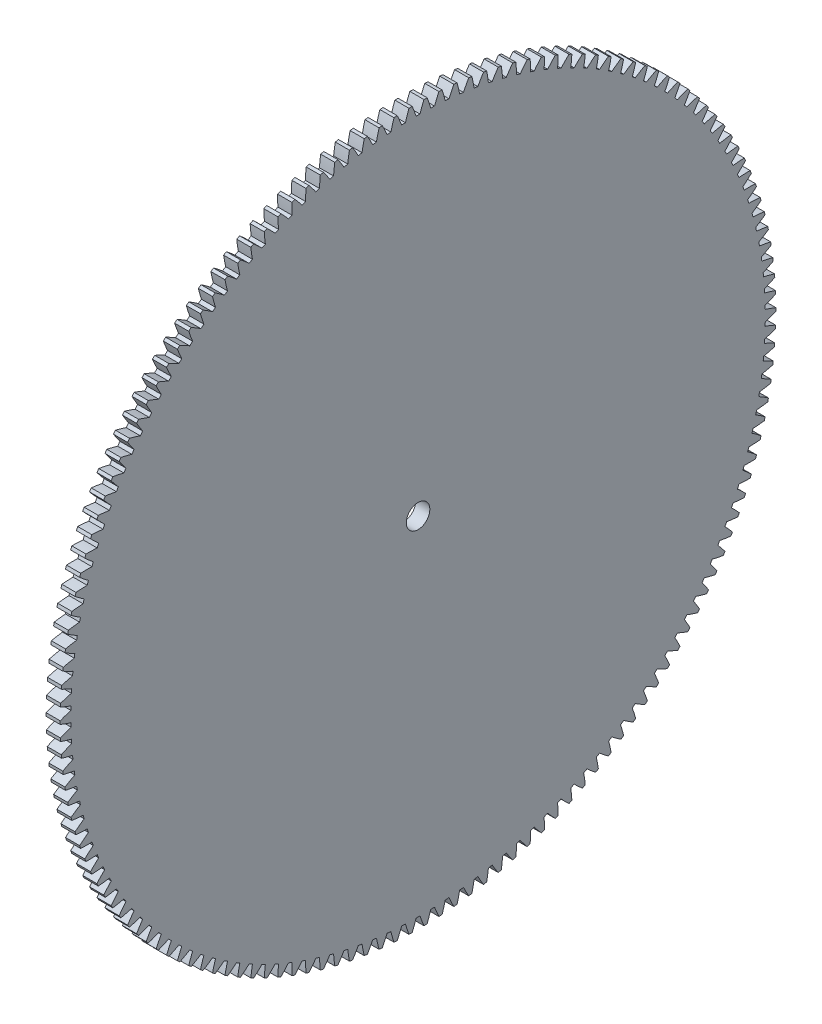
SolidWorks part; units mm, degrees
ref_plane "Plane1" through (0, 0, 0) normal (0, 0, 1) x (1, 0, 0)
ref_plane "Plane2" through (0, 0, 0) normal (0, 1, 0) x (1, 0, 0)
ref_plane "Plane3" through (0, 0, 0) normal (1, 0, 0) x (0, 0, -1)
sketch "HoldingSke" plane through (0, 0, 0) normal (0, 1, 0) x (1, 0, 0)
  line L0 (0, 0) -> (-0.866, -0.5)
  line L1 (-15, 0) -> (100, 0) construction
  line L2 (0, 0) -> (-2.1039, 2.3779)
  line L3 (0, 0) -> (-11.863, 4.5341)
  line L4 (0, 0) -> (-7.479, 4.318)
  line L5 (0, 0) -> (-46.8476, -17.4728)
  line L6 (0, 0) -> (-2.4869, -1.6779)
  line L7 (-2.1039, 2.3779) -> (8.6586, 51.2059)
  line L8 (-76.2, 54.61) -> (-75.3, 54.61)
  line L9 (-71.009, 38.7566) -> (-53.1078, 45.2721)
  line L10 (-76.2, 71.12) -> (104.1128, 71.12)
  line L11 (0, 0) -> (-3, 0)
  line L12 (-76.2, 101.6) -> (-76.162, 101.6)
  line L13 (24.9733, 27.94) -> (52.9518, 28.4284)
  line L14 (24.9733, 27.94) -> (24.9743, 27.94)
  line L15 (24.9733, 27.94) -> (100.4006, 29.5858)
  line L16 (-63.627, -1) -> (-12.827, -1)
  circle A0 centre (0, 0) radius 2.5
  circle A1 centre (0, 0) radius 37.5
  circle A2 centre (0, 0) radius 37.5
  circle A3 centre (0, 0) radius 2.5
  dimension "MHD" = 75
  dimension "Hub_dia" = 75
  dimension "Bore" = 5
  dimension "MBD" = 5
  dimension "Num_teeth" = 150
  dimension "Pitch_radius" = 180.3128
  dimension "Pitch" = 1
  dimension "Width" = 3
  dimension "Overall_len" = 50
  dimension "Show_teeth" = 150
  dimension "Thickness" = 3
  dimension "OAL" = 50.0001
  dimension "T_dim" = 0.9
  dimension "Ap" = 20
  dimension "H" = 19.05
  dimension "Backlash" = 0.038
  dimension "Addendum_fac" = 1
  dimension "Dedendum_fac" = 1.25
  dimension "Clearance_fac" = 0.25
  dimension "Dedendum_add" = 0.001
  dimension "Module" = 1
sketch "BasProSke" plane through (0, 0, 0) normal (0, 1, 0) x (1, 0, 0)
  line L0 (-10, 0) -> (60, 0) construction
  line L1 (0, 0) -> (0, 76)
  line L2 (0, 0) -> (3, 0)
  line L3 (3, 0) -> (3, 76)
  line L4 (3, 76) -> (0, 76)
  dimension "Diameter" = 152
  dimension "Thickness" = 3
revolve "Base-Revolve" add sketch "BasProSke" angle 360 about L0
sketch "TooCutSke" plane through (0, 0, 0) normal (1, 0, 0) x (0, 0, -1)
  line L1 (0, 0) -> (0, 107) construction
  line L2 (0, 0) -> (-0.8519, 74.9952) construction
  line L3 (0, 0) -> (-3.1412, 149.9602) construction
  line L4 (-0.8519, 74.9952) -> (-1.5706, 74.9801) construction
  arc A0 (0.4067, 73.7479) -> (-0.4067, 73.7479) centre (0, 0) ccw
  arc A1 (1.263, 76.0149) -> (-1.263, 76.0149) centre (0, 0) ccw
  circle A2 centre (0, 0) radius 75 construction
  circle A3 centre (0, 0) radius 70.4769 construction
  arc A4 (-0.4067, 73.7479) -> (-1.263, 76.0149) centre (-28.8767, 64.2895) ccw
  arc A5 (1.263, 76.0149) -> (0.4067, 73.7479) centre (28.8767, 64.2895) ccw
  dimension "Root_dia" = 147.498
  dimension "Overcut_dia" = 152.0508
  dimension "Pitch_dia" = 150
  dimension "Base_dia" = 140.9539
  dimension "Flank_rad" = 30
  dimension "Half_ang" = 1.2
  dimension "Half_CT" = 0.7189
extrude "ToothCut" cut sketch "TooCutSke" along normal through all
fillet "Breaks" [suppressed] radius 0.02
fillet "RootFillets" [suppressed] radius 0.251
pattern_circular "TeethCuts" count 150 every 2.4 about axis through (-10, 0, 0) along (1, 0, 0) of "ToothCut", "RootFillets", "Breaks"
sketch "HubNeaOneSke" plane through (0, 0, 0) normal (-1, 0, 0) x (0, 0, 1)
  circle A0 centre (0, 0) radius 37.5
  dimension "Diameter" = 75
extrude "HubNearOne" [suppressed] add sketch "HubNeaOneSke" along normal blind 47.0001
sketch "HubNeaBotSke" plane through (0, 0, 0) normal (-1, 0, 0) x (0, 0, 1)
  circle A0 centre (0, 0) radius 37.5
  dimension "Diameter" = 75
extrude "HubNearBoth" [suppressed] add sketch "HubNeaBotSke" along normal blind 23.5
ref_plane "FarPln" through (3, 0, 0) normal (1, 0, 0) x (0, 0, -1)
sketch "HubFarSke" plane through (3, 0, 0) normal (1, 0, 0) x (0, 0, -1)
  circle A0 centre (0, 0) radius 37.5
  dimension "Diameter" = 75
extrude "HubFar" [suppressed] add sketch "HubFarSke" along normal blind 23.5
sketch "BorSke" plane through (0, 0, 0) normal (1, 0, 0) x (0, 0, -1)
  circle A0 centre (0, 0) radius 2.5
  dimension "Diameter" = 5
extrude "Bore" cut sketch "BorSke" along normal mid plane 100.0001
sketch "KeySke" plane through (0, 0, 0) normal (1, 0, 0) x (0, 0, -1)
  line L0 (-1, 0) -> (-1, 3.4)
  line L1 (-1, 3.4) -> (1, 3.4)
  line L2 (1, 3.4) -> (1, 0)
  line L3 (0, 0) -> (0, 34) construction
  line L4 (-1, 0) -> (1, 0)
  dimension "Offset" = 3.4
  dimension "Width" = 2
extrude "Keyway" [suppressed] cut sketch "KeySke" along normal mid plane 100.0001
pattern_circular "Keyway2" [suppressed] count 2 every 90 about axis through (-10, 0, 0) along (1, 0, 0)
equation "' \"Module@HoldingSke\" = 6.35"
equation "' \"Num_teeth@HoldingSke\" = 12"
equation "' \"Ap@HoldingSke\" =  20"
equation "' \"Width@HoldingSke\" = 0.5 * 25.4"
equation "' \"Hub_dia@HoldingSke\"= 1 * 25.4"
equation "' \"Overall_len@HoldingSke\" = 1.0 * 25.4"
equation "' \"Bore@HoldingSke\" = 0.75 * 25.4"
equation "' \"T_dim@HoldingSke\" = 0.1 * 25.4"
equation "' \"Width@KeySke\" = 0.25 * 25.4"
equation "' \"Show_teeth@HoldingSke\" = 13"
equation "' \"Backlash@HoldingSke\" = 0.009 * 25.4"
equation "' \"Addendum_fac@HoldingSke\" = 1.0"
equation "' \"Dedendum_fac@HoldingSke\" = 1.25"
equation "' \"Dedendum_add@HoldingSke\" = 0.00005 * 25.4"
equation "' \"Clearance_fac@HoldingSke\" = 0.25"
equation "\"Pitch@HoldingSke\" = 1 / \"Module@HoldingSke\""
equation "\"Overcut_dia@TooCutSke\" = (\"Num_teeth@HoldingSke\" + 2 * \"Addendum_fac@HoldingSke\") / \"Pitch@HoldingSke\" + 0.002 * 25.4"
equation "\"Pitch_dia@TooCutSke\" = \"Num_teeth@HoldingSke\" / \"Pitch@HoldingSke\""
equation "\"Base_dia@TooCutSke\" = \"Num_teeth@HoldingSke\" / \"Pitch@HoldingSke\" * cos((\"Ap@HoldingSke\"  * 3.14159265 / 180))"
equation "\"Root_dia@TooCutSke\" = (\"Num_teeth@HoldingSke\" + 2) / \"Pitch@HoldingSke\" - 2 * (\"Addendum_fac@HoldingSke\" + \"Dedendum_fac@HoldingSke\") / \"Pitch@HoldingSke\" - \"Dedendum_add@HoldingSke\" * 2"
equation "\"Half_ang@TooCutSke\" = 180 / \"Num_teeth@HoldingSke\""
equation "\"Half_CT@TooCutSke\" = \"Num_teeth@HoldingSke\" / \"Pitch@HoldingSke\" * sin((3.14159265 / 2 / \"Num_teeth@HoldingSke\")) / 2 - 7 * \"Backlash@HoldingSke\" / 4"
equation "\"Flank_rad@TooCutSke\" = \"Num_teeth@HoldingSke\" / \"Pitch@HoldingSke\" / 5"
equation "\"Radius@RootFillets\" = \"Clearance_fac@HoldingSke\" / \"Pitch@HoldingSke\" + \"Dedendum_add@HoldingSke\""
equation "\"Break_rad@Breaks\" = 0.02 / \"Pitch@HoldingSke\""
equation "\"Thickness@HoldingSke\" = \"Width@HoldingSke\""
equation "\"OAL@HoldingSke\" = \"Thickness@HoldingSke\""
equation "\"MHD@HoldingSke\" = (\"Num_teeth@HoldingSke\" + 2) / \"Pitch@HoldingSke\" - 2 * (\"Addendum_fac@HoldingSke\" + \"Dedendum_fac@HoldingSke\")  / \"Pitch@HoldingSke\" - \"Dedendum_add@HoldingSke\" * 2"
equation "\"MBD@HoldingSke\" = (\"Num_teeth@HoldingSke\" + 2) / \"Pitch@HoldingSke\" - 2 * (\"Addendum_fac@HoldingSke\" + \"Dedendum_fac@HoldingSke\")  / \"Pitch@HoldingSke\" - \"Dedendum_add@HoldingSke\" * 2 - 0.002 * 25.4"
equation "\"MHD@HoldingSke\" = ((sgn( \"MHD@HoldingSke\" - \"Hub_dia@HoldingSke\" )-1)*( \"MHD@HoldingSke\" - \"Hub_dia@HoldingSke\" ))/-2+ \"Hub_dia@HoldingSke\""
equation "\"MBD@HoldingSke\" = ((sgn( \"MBD@HoldingSke\" - \"Bore@HoldingSke\" )-1)*( \"MBD@HoldingSke\" - \"Bore@HoldingSke\" ))/-2+ \"Bore@HoldingSke\""
equation "\"OAL@HoldingSke\" = ((sgn( \"OAL@HoldingSke\" - \"Overall_len@HoldingSke\" )+1)*( \"OAL@HoldingSke\" - \"Overall_len@HoldingSke\" ))/2 + \"Overall_len@HoldingSke\" + 0.000002 * 25.4"
equation "\"Num_teeth@TeethCuts\" = int( \"Show_teeth@HoldingSke\" ) + 1"
equation "\"Num_teeth@TeethCuts\" = ((sgn( \"Num_teeth@TeethCuts\" - \"Num_teeth@HoldingSke\" )-1)*( \"Num_teeth@TeethCuts\" - \"Num_teeth@HoldingSke\" ))/-2+ \"Num_teeth@HoldingSke\""
equation "\"Num_teeth@TeethCuts\" = ((sgn( \"Num_teeth@TeethCuts\" - 2.0)+1)*( \"Num_teeth@TeethCuts\" - 2.0))/2 +2.0"
equation "\"Angle@TeethCuts\" = 360.0 / \"Num_teeth@HoldingSke\""
equation "\"Diameter@BasProSke\" = (\"Num_teeth@HoldingSke\" + 2 * \"Addendum_fac@HoldingSke\") / \"Pitch@HoldingSke\""
equation "\"Thickness@BasProSke\"  = \"Thickness@HoldingSke\""
equation "' \"Fillet_rad@BasProSke\" =  \"Thickness@HoldingSke\" * 0.05"
equation "\"MHD@HoldingSke\" = ((sgn( \"MHD@HoldingSke\" - \"Root_dia@TooCutSke\" )-1)*( \"MHD@HoldingSke\" - \"Root_dia@TooCutSke\" ))/-2+ \"Root_dia@TooCutSke\""
equation "\"Diameter@HubNeaOneSke\" = \"MHD@HoldingSke\""
equation "\"Length@HubNearOne\" = \"OAL@HoldingSke\" - \"Thickness@BasProSke\""
equation "\"Diameter@HubNeaBotSke\" = \"MHD@HoldingSke\""
equation "\"Length@HubNearBoth\" = ( \"OAL@HoldingSke\" - \"Thickness@BasProSke\" ) / 2.0"
equation "\"Thickness@FarPln\" = \"Thickness@BasProSke\""
equation "\"Diameter@HubFarSke\" = \"MHD@HoldingSke\""
equation "\"Length@HubFar\" = ( \"OAL@HoldingSke\" - \"Thickness@BasProSke\" ) / 2.0"
equation "\"Diameter@BorSke\" = \"MBD@HoldingSke\""
equation "\"D1@Bore\" = \"OAL@HoldingSke\" * 2.0"
equation "\"D1@Keyway\" = \"OAL@HoldingSke\" * 2.0"
equation "\"Offset@KeySke\" = \"T_dim@HoldingSke\" + \"MBD@HoldingSke\" / 2.0"
